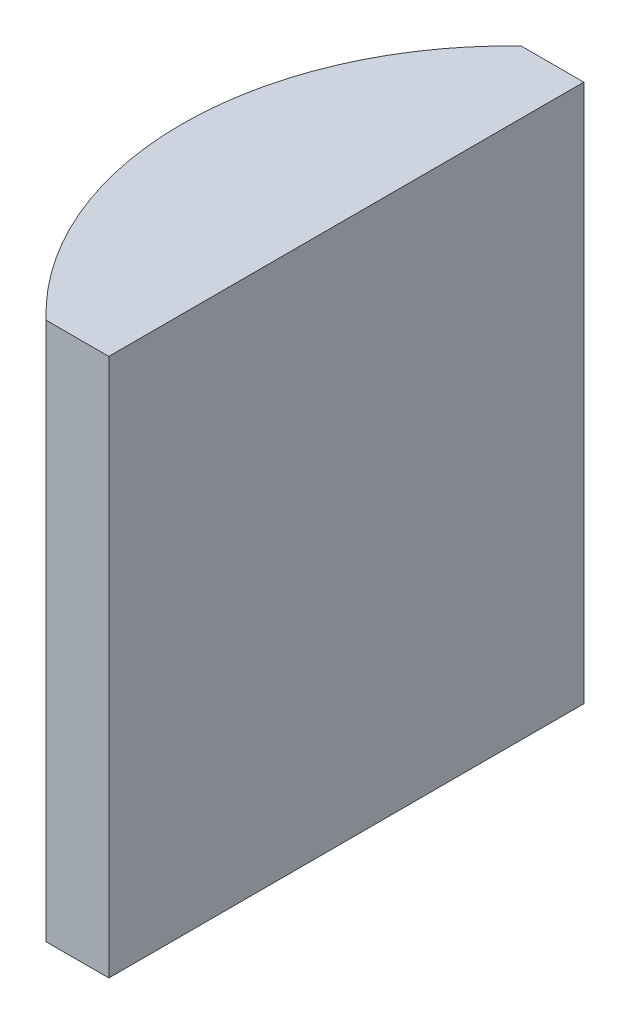
SolidWorks part; units mm, degrees
ref_plane "前视基准面" through (0, 0, 0) normal (0, 0, 1) x (1, 0, 0)
ref_plane "上视基准面" through (0, 0, 0) normal (0, 1, 0) x (1, 0, 0)
ref_plane "右视基准面" through (0, 0, 0) normal (1, 0, 0) x (0, 0, -1)
sketch "草图1" plane through (0, 0, 0) normal (0, 1, 0) x (1, 0, 0)
  line L0 (10.7432, 0) -> (-19.1624, 0) construction
  line L1 (-2.7628, 7.5) -> (-0.7848, 7.5)
  line L2 (-2.7628, -7.5) -> (-0.7848, -7.5)
  line L3 (-0.7848, 7.5) -> (-0.7848, -7.5)
  arc A0 (-2.7628, 7.5) -> (-2.7628, -7.5) centre (4.3552, 0) ccw
  point P19 (-5.9848, 0)
  point P20 (-0.7848, 0)
  dimension "D2" = 7.5
  dimension "D3" = 10.34
  dimension "D4" = 5.2
  dimension "D1" = 7.5
extrude "凸台-拉伸1" add sketch "草图1" along normal blind 17
